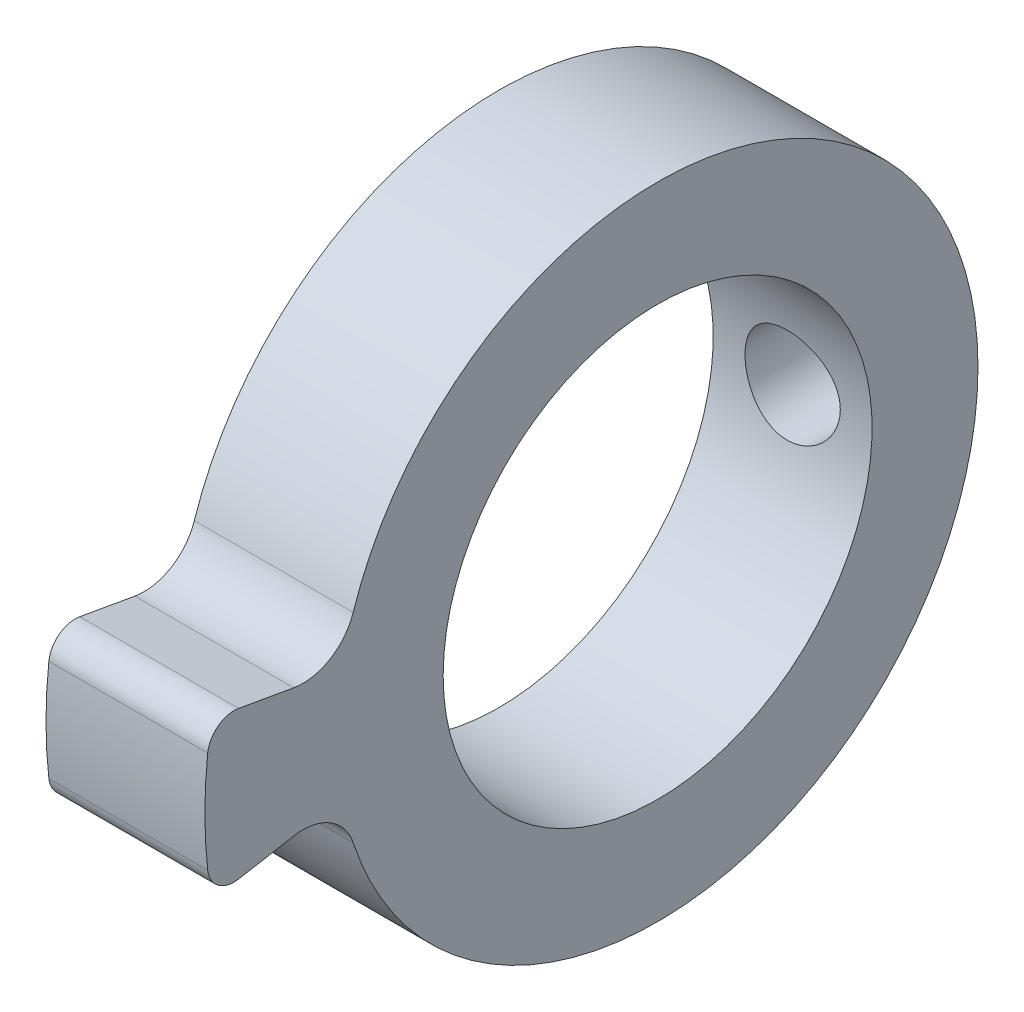
SolidWorks part; units mm, degrees
ref_plane "Plan de face" through (0, 0, 0) normal (0, 0, 1) x (1, 0, 0)
ref_plane "Plan de dessus" through (0, 0, 0) normal (0, 1, 0) x (1, 0, 0)
ref_plane "Plan de droite" through (0, 0, 0) normal (1, 0, 0) x (0, 0, -1)
sketch "Esquisse1" plane through (0, 0, 0) normal (0, 0, 1) x (1, 0, 0)
  line L0 (-3.996, 0) -> (6.4349, 0) construction
  line L1 (0, 4.05) -> (0, 6.05)
  line L2 (0, 6.05) -> (3, 6.05)
  line L3 (3, 6.05) -> (3, 4.05)
  line L6 (3, 4.05) -> (0, 4.05)
  dimension "D1" = 8.1
  dimension "D3" = 2
  dimension "D4" = 3
revolve "Révolution1" add sketch "Esquisse1" angle 360 about L0
sketch "Esquisse2" plane through (0, 0, 0) normal (-1, 0, 0) x (0, 0, 1)
  line L0 (5.9581, -1.0506) -> (8.4201, -1.4847)
  line L4 (5.9581, 1.0506) -> (8.4201, 1.4847)
  circle A4 centre (0, 0) radius 6.05 construction
  circle A5 centre (0, 0) radius 8.55
  arc A6 (8.4201, -1.4847) -> (8.4201, 1.4847) centre (0, 0) ccw
  arc A9 (5.9581, -1.0506) -> (5.9581, 1.0506) centre (0, 0) ccw
  dimension "D1" = 20
  dimension "D2" = 2.5
extrude "Boss.-Extru.1" add sketch "Esquisse2" against normal up to surface (3 mm away) up to face at (3, 0, 6.05)
fillet "Congé1" radius 1 2 edges at (1.5, -1.0506, 5.9581) (1.5, 1.0506, 5.9581)
fillet "Congé3" radius 0.5 2 edges at (1.5, 1.4847, 8.4201) (1.5, -1.4847, 8.4201)
hole_wizard "Dégagement M21" positions "Esquisse5" profile "Esquisse4" hole size "M2" standard "ISO"
sketch "Esquisse5" plane through (0, 0, 0) normal (0, 0, 1) x (1, 0, 0)
  point P0 (1.5, 0)
  dimension "D1" = 1.5
sketch "Esquisse4" plane through (1.5, 0, 0) normal (1, 0, 0) x (0, -1, 0)
  line L0 (0, 0) -> (0, 6.05)
  line L1 (0, 6.05) -> (0.9, 6.05)
  line L2 (0.9, 6.05) -> (0.9, 0)
  line L5 (0.9, 0) -> (0, 0)
  line L11 (0, -6.35) -> (0, 107.95) construction
  dimension "Diamètre du perçage jusqu'au prochain" = 1.8
  dimension "Profondeur du perçage jusqu'au prochain" = 6.05
